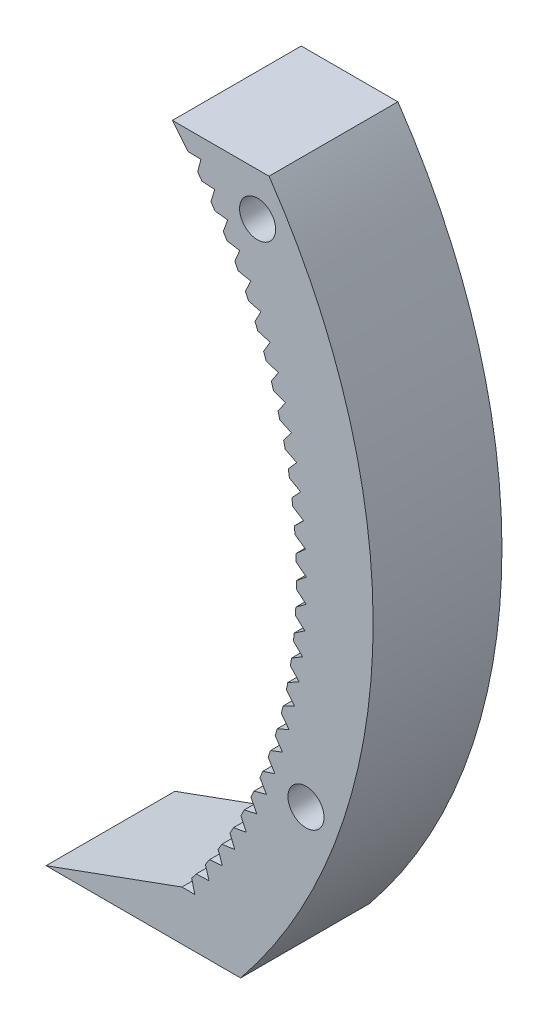
SolidWorks part; units mm, degrees
material "Alloy Steel"
ref_plane "Front" through (0, 0, 0) normal (0, 0, 1) x (1, 0, 0)
ref_plane "Top" through (0, 0, 0) normal (0, 1, 0) x (1, 0, 0)
ref_plane "Right" through (0, 0, 0) normal (1, 0, 0) x (0, 0, -1)
sketch "Sketch1" plane through (0, 0, 0) normal (0, 0, 1) x (1, 0, 0)
  circle A0 centre (0, 0) radius 21.1667
extrude "Boss-Extrude1" add sketch "Sketch1" along normal blind 12.7
sketch "Sketch3" plane through (0, 0, 0) normal (0, 0, 1) x (1, 0, 0)
  line L0 (0, 0) -> (43.7181, 0) construction
  line L2 (0, 0) -> (-0.9393, 16.3773) construction
  line L3 (0, 0) -> (0.9393, 16.3773) construction
  line L4 (0.9393, 16.3773) -> (0.9886, 17.2368) construction
  line L5 (0, 0) -> (0, 61.276) construction
  line L6 (-0.9393, 16.3773) -> (-0.9886, 17.2368) construction
  circle A0 centre (0, 0) radius 21.1667 construction
  circle A1 centre (0, 0) radius 19.05 construction
  circle A2 centre (0, 0) radius 17.2652 construction
  arc A3 (0.9393, 16.3773) -> (-0.9393, 16.3773) centre (0, 0) ccw construction
  arc A5 (3.1554, 20.9302) -> (-3.1554, 20.9302) centre (0, 0) ccw
  spline S0 degree 4 poles (-0.9886, 17.2368) (-0.9891, 17.2432) (-0.9907, 17.2612) (-0.9949, 17.295) (-1.0034, 17.35) (-1.0167, 17.4198) (-1.0366, 17.5096) (-1.0637, 17.6148) (-1.0972, 17.7297) (-1.1377, 17.8539) (-1.1816, 17.977) (-1.2287, 18.099) (-1.2785, 18.2198) (-1.3423, 18.3651) (-1.4236, 18.5381) (-1.5256, 18.738) (-1.6493, 18.9622) (-1.784, 19.1875) (-1.9235, 19.4067) (-2.0724, 19.6249) (-2.2221, 19.8338) (-2.3856, 20.0472) (-2.5406, 20.2425) (-2.7229, 20.4571) (-2.8726, 20.6291) (-3.0791, 20.8514) (-3.2038, 20.9813) (-3.3529, 21.1316) (-3.4207, 21.1975) (-3.4624, 21.2381) knots 0 0 0 0 0 0.005377 0.015084 0.028532 0.04661 0.064855 0.092111 0.119476 0.146842 0.174209 0.201575 0.228941 0.256307 0.307035 0.361767 0.4165 0.471232 0.525964 0.580697 0.635429 0.690161 0.744894 0.799626 0.854358 0.909091 0.954545 1 1 1 1 1 construction
  spline S1 degree 4 poles (-0.9886, 17.2368) (-0.9891, 17.2432) (-0.9907, 17.2612) (-0.9949, 17.295) (-1.0034, 17.35) (-1.0167, 17.4198) (-1.0366, 17.5096) (-1.0637, 17.6148) (-1.0972, 17.7297) (-1.1377, 17.8539) (-1.1816, 17.977) (-1.2287, 18.099) (-1.2785, 18.2198) (-1.3423, 18.3651) (-1.4236, 18.5381) (-1.5256, 18.738) (-1.6493, 18.9622) (-1.784, 19.1875) (-1.9235, 19.4067) (-2.0724, 19.6249) (-2.2221, 19.8338) (-2.3856, 20.0472) (-2.5406, 20.2425) (-2.7229, 20.4571) (-2.8726, 20.6291) (-3.0344, 20.8032) (-3.1141, 20.8874) (-3.1554, 20.9302) knots 0 0 0 0 0 0.005377 0.015084 0.028532 0.04661 0.064855 0.092111 0.119476 0.146842 0.174209 0.201575 0.228941 0.256307 0.307035 0.361767 0.4165 0.471232 0.525964 0.580697 0.635429 0.690161 0.744894 0.799626 0.854358 0.909091 0.909091 0.909091 0.909091 0.909091
  spline S2 degree 4 poles (0.9886, 17.2368) (0.9891, 17.2432) (0.9907, 17.2612) (0.9949, 17.295) (1.0034, 17.35) (1.0167, 17.4198) (1.0366, 17.5096) (1.0637, 17.6148) (1.0972, 17.7297) (1.1377, 17.8539) (1.1816, 17.977) (1.2287, 18.099) (1.2785, 18.2198) (1.3423, 18.3651) (1.4236, 18.5381) (1.5256, 18.738) (1.6493, 18.9622) (1.784, 19.1875) (1.9235, 19.4067) (2.0724, 19.6249) (2.2221, 19.8338) (2.3856, 20.0472) (2.5406, 20.2425) (2.7229, 20.4571) (2.8726, 20.6291) (3.0791, 20.8514) (3.2038, 20.9813) (3.3529, 21.1316) (3.4207, 21.1975) (3.4624, 21.2381) knots 0 0 0 0 0 0.005377 0.015084 0.028532 0.04661 0.064855 0.092111 0.119476 0.146842 0.174209 0.201575 0.228941 0.256307 0.307035 0.361767 0.4165 0.471232 0.525964 0.580697 0.635429 0.690161 0.744894 0.799626 0.854358 0.909091 0.954545 1 1 1 1 1 construction
  spline S3 degree 4 poles (0.9886, 17.2368) (0.9891, 17.2432) (0.9907, 17.2612) (0.9949, 17.295) (1.0034, 17.35) (1.0167, 17.4198) (1.0366, 17.5096) (1.0637, 17.6148) (1.0972, 17.7297) (1.1377, 17.8539) (1.1816, 17.977) (1.2287, 18.099) (1.2785, 18.2198) (1.3423, 18.3651) (1.4236, 18.5381) (1.5256, 18.738) (1.6493, 18.9622) (1.784, 19.1875) (1.9235, 19.4067) (2.0724, 19.6249) (2.2221, 19.8338) (2.3856, 20.0472) (2.5406, 20.2425) (2.7229, 20.4571) (2.8726, 20.6291) (3.0344, 20.8032) (3.1141, 20.8874) (3.1554, 20.9302) knots 0 0 0 0 0 0.005377 0.015084 0.028532 0.04661 0.064855 0.092111 0.119476 0.146842 0.174209 0.201575 0.228941 0.256307 0.307035 0.361767 0.4165 0.471232 0.525964 0.580697 0.635429 0.690161 0.744894 0.799626 0.854358 0.909091 0.909091 0.909091 0.909091 0.909091
  point P0 (0, 16.4042)
sketch "DCLTBC" plane through (0, 0, 0) normal (0, 0, 1) x (1, 0, 0)
  line L0 (0, 0) -> (41.04, 0) construction
  line L1 (-0.9393, 16.3773) -> (-0.9886, 17.2368) construction
  line L2 (0.9393, 16.3773) -> (0.9886, 17.2368) construction
  line L3 (-0.9393, 16.3773) -> (-0.9886, 17.2368)
  line L4 (0.9393, 16.3773) -> (0.9886, 17.2368)
  line L5 (0, 0) -> (0, 104.9356) construction
  circle A0 centre (0, 0) radius 21.1667
  circle A1 centre (0, 0) radius 19.05 construction
  circle A2 centre (0, 0) radius 17.2652 construction
  arc A3 (0.9393, 16.3773) -> (-0.9393, 16.3773) centre (0, 0) ccw construction
  arc A4 (0.9393, 16.3773) -> (-0.9393, 16.3773) centre (0, 0) ccw
  spline S0 degree 4 poles (-998.2859, -55.9585) (-15.2714, 14.5763) (-1.1564, 16.0258) (-0.9033, 16.703) (-1.0034, 17.35) (-1.0167, 17.4198) (-1.0366, 17.5096) (-1.0637, 17.6148) (-1.0972, 17.7297) (-1.1377, 17.8539) (-1.1816, 17.977) (-1.2287, 18.099) (-1.2785, 18.2198) (-1.3423, 18.3651) (-1.4236, 18.5381) (-1.5256, 18.738) (-1.6493, 18.9622) (-1.784, 19.1875) (-1.9235, 19.4067) (-2.0724, 19.6249) (-2.2221, 19.8338) (-2.3856, 20.0472) (-2.5406, 20.2425) (-2.7229, 20.4571) (-3.4042, 21.2399) (-5.6764, 23.4628) (17.3745, -0.7418) (-697.1444, 740.8893) knots -0.501613 -0.501613 -0.501613 -0.501613 -0.501613 0.005377 0.015084 0.028532 0.04661 0.064855 0.092111 0.119476 0.146842 0.174209 0.201575 0.228941 0.256307 0.307035 0.361767 0.4165 0.471232 0.525964 0.580697 0.635429 0.690161 0.744894 0.799626 0.854358 1.68661 1.68661 1.68661 1.68661 1.68661 only from (-0.9886, 17.2368) to (-3.1554, 20.9302) construction
  spline S1 degree 4 poles (998.2859, -55.9585) (15.2714, 14.5763) (1.1564, 16.0258) (0.9033, 16.703) (1.0034, 17.35) (1.0167, 17.4198) (1.0366, 17.5096) (1.0637, 17.6148) (1.0972, 17.7297) (1.1377, 17.8539) (1.1816, 17.977) (1.2287, 18.099) (1.2785, 18.2198) (1.3423, 18.3651) (1.4236, 18.5381) (1.5256, 18.738) (1.6493, 18.9622) (1.784, 19.1875) (1.9235, 19.4067) (2.0724, 19.6249) (2.2221, 19.8338) (2.3856, 20.0472) (2.5406, 20.2425) (2.7229, 20.4571) (3.4042, 21.2399) (5.6764, 23.4628) (-17.3745, -0.7418) (697.1444, 740.8893) knots -0.501613 -0.501613 -0.501613 -0.501613 -0.501613 0.005377 0.015084 0.028532 0.04661 0.064855 0.092111 0.119476 0.146842 0.174209 0.201575 0.228941 0.256307 0.307035 0.361767 0.4165 0.471232 0.525964 0.580697 0.635429 0.690161 0.744894 0.799626 0.854358 1.68661 1.68661 1.68661 1.68661 1.68661 only from (0.9886, 17.2368) to (3.1554, 20.9302) construction
  spline S2 degree 4 poles (-0.9886, 17.2368) (-0.9891, 17.2432) (-0.9907, 17.2612) (-0.9949, 17.295) (-1.0034, 17.35) (-1.0167, 17.4198) (-1.0366, 17.5096) (-1.0637, 17.6148) (-1.0972, 17.7297) (-1.1377, 17.8539) (-1.1816, 17.977) (-1.2287, 18.099) (-1.2785, 18.2198) (-1.3423, 18.3651) (-1.4236, 18.5381) (-1.5256, 18.738) (-1.6493, 18.9622) (-1.784, 19.1875) (-1.9235, 19.4067) (-2.0724, 19.6249) (-2.2221, 19.8338) (-2.3856, 20.0472) (-2.5406, 20.2425) (-2.7229, 20.4571) (-2.8726, 20.6291) (-3.0344, 20.8032) (-3.1141, 20.8874) (-3.1554, 20.9302) knots 0 0 0 0 0 0.005377 0.015084 0.028532 0.04661 0.064855 0.092111 0.119476 0.146842 0.174209 0.201575 0.228941 0.256307 0.307035 0.361767 0.4165 0.471232 0.525964 0.580697 0.635429 0.690161 0.744894 0.799626 0.854358 0.909091 0.909091 0.909091 0.909091 0.909091
  spline S3 degree 4 poles (0.9886, 17.2368) (0.9891, 17.2432) (0.9907, 17.2612) (0.9949, 17.295) (1.0034, 17.35) (1.0167, 17.4198) (1.0366, 17.5096) (1.0637, 17.6148) (1.0972, 17.7297) (1.1377, 17.8539) (1.1816, 17.977) (1.2287, 18.099) (1.2785, 18.2198) (1.3423, 18.3651) (1.4236, 18.5381) (1.5256, 18.738) (1.6493, 18.9622) (1.784, 19.1875) (1.9235, 19.4067) (2.0724, 19.6249) (2.2221, 19.8338) (2.3856, 20.0472) (2.5406, 20.2425) (2.7229, 20.4571) (2.8726, 20.6291) (3.0344, 20.8032) (3.1141, 20.8874) (3.1554, 20.9302) knots 0 0 0 0 0 0.005377 0.015084 0.028532 0.04661 0.064855 0.092111 0.119476 0.146842 0.174209 0.201575 0.228941 0.256307 0.307035 0.361767 0.4165 0.471232 0.525964 0.580697 0.635429 0.690161 0.744894 0.799626 0.854358 0.909091 0.909091 0.909091 0.909091 0.909091
extrude "Cut-Extrude-DCLTBC" cut sketch "DCLTBC" along normal through all
fillet "Fillet-Tip-DCLTBC" radius 0.3764 2 edges at (3.1554, 20.9302, 6.35) (-3.1554, 20.9302, 6.35)
fillet "Fillet-Root-DCLTBC" radius 0.7528 2 edges at (-0.9393, 16.3773, 6.35) (0.9393, 16.3773, 6.35)
pattern_circular "CirPattern-DCLTBC" count 18 over 360 about axis through (0, 0, 12.7) along (0, 0, 1) of "Cut-Extrude-DCLTBC", "Fillet-Tip-DCLTBC", "Fillet-Root-DCLTBC"
sketch "DCGTBC" [suppressed] plane through (0, 0, 0) normal (0, 0, 1) x (1, 0, 0)
  line L0 (0, 0) -> (41.04, 0) construction
  line L1 (-22.6634, 1.9828) -> (0, 0) construction
  line L2 (0, 0) -> (22.6634, 1.9828) construction
  line L3 (0, 0) -> (-16.5124, 0)
  line L5 (0, 0) -> (0, 104.9356) construction
  circle A0 centre (0, 0) radius 25
  circle A1 centre (0, 0) radius 24 construction
  circle A2 centre (0, 0) radius 21.7514 construction
  arc A3 (0.0626, 22.7499) -> (-0.0626, 22.7499) centre (0, 0) ccw construction
  arc A11 (22.6634, 1.9828) -> (-22.6634, 1.9828) centre (0, 0) ccw
  spline S4 degree 4 poles (999.7589, -2.0808) (12.8658, 20.0937) (0.2547, 20.6746) (0.0189, 21.2606) (0.0654, 21.8429) (0.0715, 21.8997) (0.0812, 21.973) (0.095, 22.0592) (0.1126, 22.1539) (0.1343, 22.2566) (0.1583, 22.3589) (0.1845, 22.4607) (0.2124, 22.562) (0.2486, 22.6844) (0.2952, 22.8308) (0.3543, 23.0013) (0.4268, 23.1939) (0.5065, 23.3893) (0.5897, 23.5809) (0.6793, 23.7735) (0.7698, 23.9592) (0.8695, 24.151) (0.9643, 24.3275) (1.0767, 24.524) (1.517, 25.277) (3.0654, 27.5692) (-13.787, 0.9944) (540.7091, 867.0187) knots -0.561807 -0.561807 -0.561807 -0.561807 -0.561807 0.005377 0.015084 0.028532 0.04661 0.064855 0.092111 0.119476 0.146842 0.174209 0.201575 0.228941 0.256307 0.307035 0.361767 0.4165 0.471232 0.525964 0.580697 0.635429 0.690161 0.744894 0.799626 0.854358 1.731906 1.731906 1.731906 1.731906 1.731906 only from (0.0598, 21.7513) to (1.3455, 24.9638) construction
  spline S5 degree 4 poles (-999.7589, -2.0808) (-12.8658, 20.0937) (-0.2547, 20.6746) (-0.0189, 21.2606) (-0.0654, 21.8429) (-0.0715, 21.8997) (-0.0812, 21.973) (-0.095, 22.0592) (-0.1126, 22.1539) (-0.1343, 22.2566) (-0.1583, 22.3589) (-0.1845, 22.4607) (-0.2124, 22.562) (-0.2486, 22.6844) (-0.2952, 22.8308) (-0.3543, 23.0013) (-0.4268, 23.1939) (-0.5065, 23.3893) (-0.5897, 23.5809) (-0.6793, 23.7735) (-0.7698, 23.9592) (-0.8695, 24.151) (-0.9643, 24.3275) (-1.0767, 24.524) (-1.517, 25.277) (-3.0654, 27.5692) (13.787, 0.9944) (-540.7091, 867.0187) knots -0.561807 -0.561807 -0.561807 -0.561807 -0.561807 0.005377 0.015084 0.028532 0.04661 0.064855 0.092111 0.119476 0.146842 0.174209 0.201575 0.228941 0.256307 0.307035 0.361767 0.4165 0.471232 0.525964 0.580697 0.635429 0.690161 0.744894 0.799626 0.854358 1.731906 1.731906 1.731906 1.731906 1.731906 only from (-0.0598, 21.7513) to (-1.3455, 24.9638) construction
  spline S6 degree 4 poles (0.0598, 21.7513) (0.0599, 21.7565) (0.0603, 21.7709) (0.0618, 21.7983) (0.0654, 21.8429) (0.0715, 21.8997) (0.0812, 21.973) (0.095, 22.0592) (0.1126, 22.1539) (0.1343, 22.2566) (0.1583, 22.3589) (0.1845, 22.4607) (0.2124, 22.562) (0.2486, 22.6844) (0.2952, 22.8308) (0.3543, 23.0013) (0.4268, 23.1939) (0.5065, 23.3893) (0.5897, 23.5809) (0.6793, 23.7735) (0.7698, 23.9592) (0.8695, 24.151) (0.9643, 24.3275) (1.0767, 24.524) (1.1693, 24.6823) (1.27, 24.8447) (1.3197, 24.9235) (1.3455, 24.9638) knots 0 0 0 0 0 0.005377 0.015084 0.028532 0.04661 0.064855 0.092111 0.119476 0.146842 0.174209 0.201575 0.228941 0.256307 0.307035 0.361767 0.4165 0.471232 0.525964 0.580697 0.635429 0.690161 0.744894 0.799626 0.854358 0.909091 0.909091 0.909091 0.909091 0.909091
  spline S7 degree 4 poles (-0.0598, 21.7513) (-0.0599, 21.7565) (-0.0603, 21.7709) (-0.0618, 21.7983) (-0.0654, 21.8429) (-0.0715, 21.8997) (-0.0812, 21.973) (-0.095, 22.0592) (-0.1126, 22.1539) (-0.1343, 22.2566) (-0.1583, 22.3589) (-0.1845, 22.4607) (-0.2124, 22.562) (-0.2486, 22.6844) (-0.2952, 22.8308) (-0.3543, 23.0013) (-0.4268, 23.1939) (-0.5065, 23.3893) (-0.5897, 23.5809) (-0.6793, 23.7735) (-0.7698, 23.9592) (-0.8695, 24.151) (-0.9643, 24.3275) (-1.0767, 24.524) (-1.1693, 24.6823) (-1.27, 24.8447) (-1.3197, 24.9235) (-1.3455, 24.9638) knots 0 0 0 0 0 0.005377 0.015084 0.028532 0.04661 0.064855 0.092111 0.119476 0.146842 0.174209 0.201575 0.228941 0.256307 0.307035 0.361767 0.4165 0.471232 0.525964 0.580697 0.635429 0.690161 0.744894 0.799626 0.854358 0.909091 0.909091 0.909091 0.909091 0.909091
  dimension "D1" = 5
  dimension "D2" = 5
extrude "Cut-Extrude-DCGTBC" [suppressed] cut sketch "DCGTBC" along normal through all
fillet "Fillet-Tip-DCGTBC" [suppressed] radius 0.3764
pattern_circular "CirPattern-DCGTBC" [suppressed] count 18 over 360
sketch "Sketch4" plane through (0, 0, 12.7) normal (0, 0, 1) x (1, 0, 0)
  circle A1 centre (0, 0) radius 3.556
  dimension "D1" = 7.112
extrude "Cut-Extrude2" cut sketch "Sketch4" against normal through all
sketch "Sketch5" plane through (0, 0, 12.7) normal (0, 0, 1) x (1, 0, 0)
  circle A0 centre (-7, 0) radius 1
  circle A1 centre (0, 7) radius 1
  circle A2 centre (7, 0) radius 1
  circle A3 centre (0, -7) radius 1
  point P12 (0, 0)
  dimension "D2" = 2
  dimension "D1" = 7
  dimension "D3" = 4
extrude "Cut-Extrude3" cut sketch "Sketch5" against normal through all
sketch "Sketch7" plane through (0, 0, 12.7) normal (0, 0, 1) x (1, 0, 0)
  line L0 (6.35, -14.1137) -> (6.35, -26.8137)
  line L2 (-3.175, -26.8137) -> (-3.175, -14.1137)
  line L3 (-3.175, -14.1137) -> (6.35, -14.1137)
  line L4 (-2.2365, -91.7884) -> (-15.6293, -96.6637)
  line L5 (-15.6293, -96.6637) -> (3.5477, -96.6637)
  arc A0 (-3.175, -26.8137) -> (-2.2365, -91.7884) centre (-41.7528, -59.8651) cw
  arc A1 (6.35, -26.8137) -> (3.5477, -96.6637) centre (-41.7528, -59.8651) cw
  dimension "D3" = 50.8
  dimension "D1" = 9.525
  dimension "D2" = 12.7
  dimension "D4" = 82.55
  dimension "D5" = 3.175
  dimension "D6" = 77.6747
  dimension "D7" = 19.177
extrude "Boss-Extrude3" add sketch "Sketch7" against normal through all
sketch "Sketch9" plane through (0, 0, 12.7) normal (0, 0, 1) x (1, 0, 0)
  circle A0 centre (5.2228, -31.0331) radius 1.778
  arc A1 (3.5477, -96.6637) -> (6.35, -26.8137) centre (-41.7528, -59.8651) ccw construction
  circle A2 centre (9.9936, -78.8467) radius 1.778
  arc A3 (-2.2365, -91.7884) -> (-3.175, -26.8137) centre (-41.7528, -59.8651) ccw construction
  dimension "D1" = 3.556
  dimension "D2" = 55.118
  dimension "D3" = 3.556
  dimension "D4" = 55.118
extrude "Cut-Extrude4" cut sketch "Sketch9" against normal blind 101.6
sketch "Sketch10" plane through (0, 0, 12.7) normal (0, 0, 1) x (1, 0, 0)
  circle A0 centre (-7, 0) radius 2.75
  circle A1 centre (0, -7) radius 2.75
  circle A2 centre (7, 0) radius 2.75
  circle A3 centre (0, 7) radius 2.75
  dimension "D1" = 5.5
extrude "Cut-Extrude5" cut sketch "Sketch10" against normal blind 7.7
sketch "Sketch11" plane through (0, 0, 12.7) normal (0, 0, 1) x (1, 0, 0)
  line L0 (-2.2365, -91.7884) -> (-0.9665, -91.7884)
  line L1 (-0.9665, -91.7884) -> (-1.2716, -90.5556)
  arc A0 (-2.2365, -91.7884) -> (-3.175, -26.8137) centre (-41.7528, -59.8651) ccw construction
  arc A1 (-2.2365, -91.7884) -> (-1.2716, -90.5556) centre (-41.7528, -59.8651) ccw
  dimension "D1" = 1.27
  dimension "D2" = 1.27
extrude "Cut-Extrude6" cut sketch "Sketch11" against normal through all
pattern_circular "CirPattern1" count 30 over 75 about axis through (-41.7528, -59.8651, 0) along (0, 0, 1) of "Cut-Extrude6"
sketch "Sketch12" plane through (0, 0, 12.7) normal (0, 0, 1) x (1, 0, 0)
  line L1 (-25.8657, -26.8137) -> (29.0619, -26.8137)
  line L2 (-25.8657, -26.8137) -> (-25.8657, 22.0423)
  line L3 (-25.8657, 22.0423) -> (29.0619, 22.0423)
  line L4 (29.0619, -26.8137) -> (29.0619, 22.0423)
extrude "Cut-Extrude7" cut sketch "Sketch12" against normal through all
equation "\"DiametralPitch\"= 12'Diametral Pitch"
equation "\"NumTeeth\"= 18'Number of Teeth"
equation "\"PressureAngle\"= 25deg'Pressure Angle"
equation "\"Addendum\"= 1 / \"DiametralPitch\"'Addendum"
equation "\"Dedendum\"= 1.25 / \"DiametralPitch\"'Dedendum"
equation "\"WorkingDepth\"= 2 / \"DiametralPitch\"'Working Depth - here for REF (Not used in building model)"
equation "\"WholeDepth\"= 2.25 / \"DiametralPitch\"'Whole Depth - here for REF (Not used in building model)"
equation "\"Clearance\"= .25 / \"DiametralPitch\"'Clearance"
equation "\"CircularPitch\"= pi / \"DiametralPitch\"'Circular Pitch - here for REF (Not used in building model)"
equation "\"PitchCircle\"= \"NumTeeth\" / \"DiametralPitch\"'Pitch Circle - or - Pitch Diameter"
equation "\"OutsideDiameter\"= ( \"NumTeeth\" + 2 ) / \"DiametralPitch\"'Outside Diameter"
equation "\"Fillet_Root\"= \"Clearance\" * cos ( \"PressureAngle\" ) * tan ( ( 90 + \"PressureAngle\" ) / 2 ) 'Fillet Root"
equation "\"AddendumCircle\"= \"PitchCircle\" + ( 2 * \"Addendum\" )'Addendum Circle - or - Addendum Diameter"
equation "\"DedendumCircle\"= \"PitchCircle\" - ( 2 * \"Dedendum\" )'Dedendum Circle - or - Dedendum Diameter"
equation "\"BaseCircle\"= \"PitchCircle\" * cos ( \"PressureAngle\" )'Base Circle - Base Diameter"
equation "\"PitchAngle\"= 360deg / \"NumTeeth\"'Pitch Angle"
equation "\"Alpha\"= sqr ( \"PitchCircle\" ^ 2 - \"BaseCircle\" ^ 2 ) / \"BaseCircle\" * 180 / PI - \"PressureAngle\"'Alpha - Used for Calculating Beta"
equation "\"Beta\"= ( \"PitchAngle\" / 4 - ( \"Alpha\" - 90 ) )'Beta - Used in definition of the parameters for the parametric equation driven curve"
equation "\"Gamma\"= ( \"PitchAngle\" / 4 - ( \"Alpha\" + 90 ) )'Gamma - Used in definition of the parameters for the parametric equation driven curve"
equation "\"Phi\"= sqr ( ( \"AddendumCircle\" / 2 ) ^ 2 - ( \"BaseCircle\" / 2 ) ^ 2 ) / ( \"BaseCircle\" / 2 )'Phi - Used in definition of the parameters for the parametric equation driven curve"
equation "\"DCGTBC\"= iif ( \"DedendumCircle\" > \"BaseCircle\" , \"unsuppressed\" , \"suppressed\" )'if Dedendum Circle IS GREATER THAN BaseCircle THEN UnsuppressORSuppress FEATURE"
equation "\"DCLTBC\"= iif ( \"DedendumCircle\" - .002 > \"BaseCircle\" , \"suppressed\" , \"unsuppressed\" )'if Dedendum Circle - .002 IS GREATER THAN BaseCircle THEN SuppressORUnsuppress FEATURE"
equation "\"Cut-Extrude-DCGTBC\"= iif ( \"DedendumCircle\" > \"BaseCircle\" , \"unsuppressed\" , \"suppressed\" )'if Dedendum Circle IS GREATER THAN BaseCircle THEN UnsuppressORSuppress FEATURE"
equation "\"Cut-Extrude-DCLTBC\"= iif ( \"DedendumCircle\" - .002 > \"BaseCircle\" , \"suppressed\" , \"unsuppressed\" )'if Dedendum Circle - .002 IS GREATER THAN BaseCircle THEN SuppressORUnsuppress FEATURE"
equation "\"CirPattern-DCGTBC\"= iif ( \"DedendumCircle\" > \"BaseCircle\" , \"unsuppressed\" , \"suppressed\" )'if Dedendum Circle IS GREATER THAN BaseCircle THEN UnsuppressORSuppress FEATURE"
equation "\"CirPattern-DCLTBC\"= iif ( \"DedendumCircle\" - .002 > \"BaseCircle\" , \"suppressed\" , \"unsuppressed\" )'if Dedendum Circle - .002 IS GREATER THAN BaseCircle THEN SuppressORUnsuppress FEATURE"
equation "\"Fillet-Tip-DCGTBC\"= iif ( \"DedendumCircle\" > \"BaseCircle\" , \"unsuppressed\" , \"suppressed\" )'if Dedendum Circle IS GREATER THAN BaseCircle THEN UnsuppressORSuppress FEATURE"
equation "\"Fillet-Tip-DCLTBC\"= iif ( \"DedendumCircle\" - .002 > \"BaseCircle\" , \"suppressed\" , \"unsuppressed\" )'if Dedendum Circle - .002 IS GREATER THAN BaseCircle THEN SuppressORUnsuppress FEATURE"
equation "\"Fillet-Root-DCLTBC\"= iif ( \"DedendumCircle\" - .002 > \"BaseCircle\" , \"suppressed\" , \"unsuppressed\" )'if Dedendum Circle - .002 IS GREATER THAN BaseCircle THEN SuppressORUnsuppress FEATURE"
equation "\"D1@CirPattern-DCGTBC\"= \"NumTeeth\"'Number of Teeth"
equation "\"D1@CirPattern-DCLTBC\"= \"NumTeeth\"'Number of Teeth"
equation "\"D1@Fillet-Tip-DCGTBC\"= \"Fillet_Root\" / 2 'Tip Rad For Large No of Teeth"
equation "\"D1@Fillet-Tip-DCLTBC\"=\"Fillet_Root\" / 2'Tip Rad For Small No of Teeth"
equation "\"D1@Fillet-Root-DCLTBC\"= \"Fillet_Root\"'Fillet Root"
